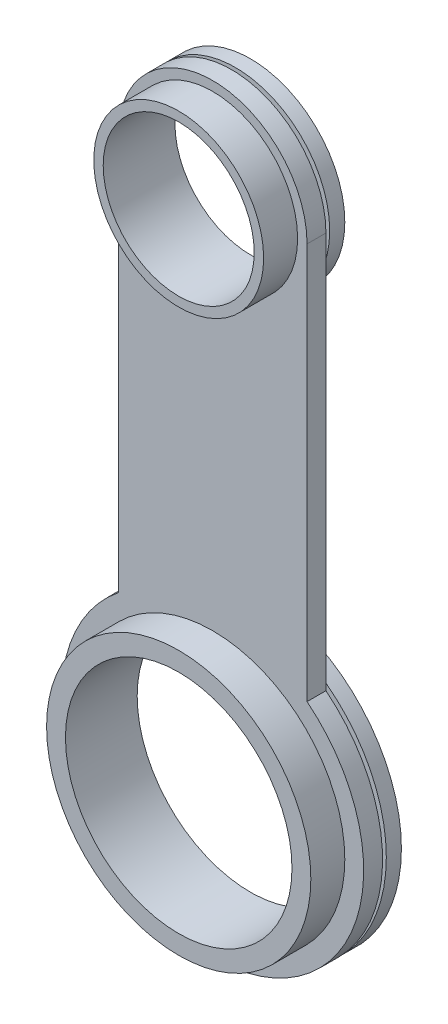
SolidWorks part; units mm, degrees
ref_plane "Alzado" through (0, 0, 0) normal (0, 0, 1) x (1, 0, 0)
ref_plane "Planta" through (0, 0, 0) normal (0, 1, 0) x (1, 0, 0)
ref_plane "Vista lateral" through (0, 0, 0) normal (1, 0, 0) x (0, 0, -1)
sketch "Croquis1" plane through (0, 0, 0) normal (0, 0, 1) x (1, 0, 0)
  line L0 (-10, -12.9388) -> (-10, -33.9388)
  line L2 (0, -33.9388) -> (0, -12.9388)
  arc A0 (-10, -33.9388) -> (0, -33.9388) centre (-5, -40.1838) ccw
  circle A1 centre (-5, -40.1838) radius 6
  arc A2 (0, -12.9388) -> (-10, -12.9388) centre (-5, -12.9388) ccw
  circle A3 centre (-5, -12.9388) radius 4
extrude "Saliente-Extruir1" add sketch "Croquis1" along normal blind 1
sketch "Croquis2" plane through (0, 0, 1) normal (0, 0, 1) x (1, 0, 0)
  circle A0 centre (-5, -40.1838) radius 7
  circle A1 centre (-5, -40.1838) radius 6 construction
  circle A2 centre (-5, -40.1838) radius 6
  circle A3 centre (-5, -12.9388) radius 4.5
  circle A5 centre (-5, -12.9388) radius 4 construction
  circle A6 centre (-5, -12.9388) radius 4
extrude "Saliente-Extruir2" add sketch "Croquis2" along normal blind 1.8
sketch "Croquis3" plane through (0, 0, 0) normal (0, 0, -1) x (-1, 0, 0)
  circle A0 centre (5, -40.1838) radius 7
  circle A1 centre (5, -40.1838) radius 6 construction
  circle A2 centre (5, -40.1838) radius 6
  circle A3 centre (5, -12.9388) radius 4.5
  circle A4 centre (5, -12.9388) radius 4 construction
  circle A5 centre (5, -12.9388) radius 4
extrude "Saliente-Extruir3" add sketch "Croquis3" along normal blind 0.2
sketch "Croquis4" plane through (0, 0, -0.2) normal (0, 0, -1) x (-1, 0, 0)
  circle A0 centre (5, -40.1838) radius 7.999
  circle A1 centre (5, -40.1838) radius 6 construction
  circle A2 centre (5, -40.1838) radius 6
  circle A3 centre (5, -12.9388) radius 4 construction
  circle A4 centre (5, -12.9388) radius 4
  circle A5 centre (5, -12.9388) radius 5
extrude "Saliente-Extruir4" add sketch "Croquis4" along normal blind 0.8
